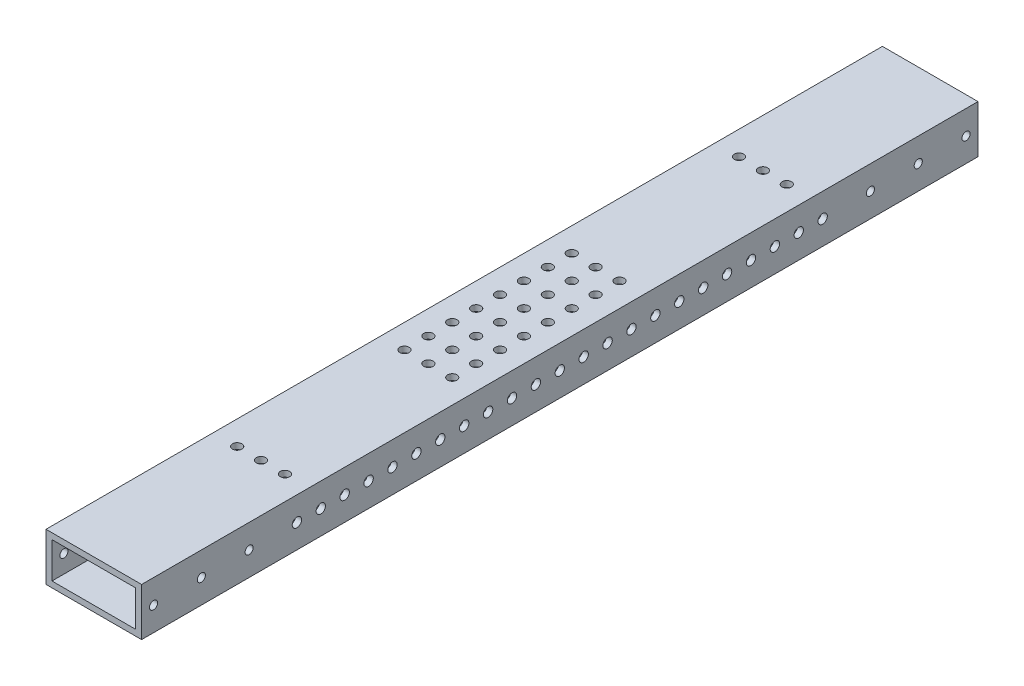
SolidWorks part; units mm, degrees
material "6061-T6 (SS)"
ref_plane "Front Plane" through (0, 0, 0) normal (0, 0, 1) x (1, 0, 0)
ref_plane "Top Plane" through (0, 0, 0) normal (0, 1, 0) x (1, 0, 0)
ref_plane "Right Plane" through (0, 0, 0) normal (1, 0, 0) x (0, 0, -1)
sketch "Sketch1" plane through (0, 0, 0) normal (0, 0, 1) x (1, 0, 0)
  line L0 (-22.225, 9.525) -> (22.225, 9.525)
  line L1 (-25.4, 12.7) -> (25.4, 12.7)
  line L2 (-25.4, 12.7) -> (-25.4, -12.7)
  line L3 (-25.4, -12.7) -> (25.4, -12.7)
  line L4 (25.4, 12.7) -> (25.4, -12.7)
  line L5 (22.225, 9.525) -> (22.225, -9.525)
  line L6 (-22.225, -9.525) -> (22.225, -9.525)
  line L7 (-22.225, 9.525) -> (-22.225, -9.525)
  line L8 (-25.4, 12.7) -> (25.4, -12.7) construction
  line L9 (25.4, 12.7) -> (-25.4, -12.7) construction
  point P5 (0, 0)
  dimension "D1" = 50.8
  dimension "D2" = 25.4
  dimension "D3" = 3.175
extrude "Boss-Extrude1" add sketch "Sketch1" along normal mid plane 444.5
sketch "Sketch3" plane through (25.4, 0, 0) normal (1, 0, 0) x (0, 0, -1)
  line L0 (-222.25, -12.7) -> (-222.25, 12.7) construction
  line L1 (-222.25, 12.7) -> (222.25, 12.7) construction
  line L2 (222.25, -12.7) -> (222.25, 12.7) construction
  circle A0 centre (-215.9, 0) radius 2.1527
  circle A1 centre (-190.5, 0) radius 2.1527
  circle A2 centre (-165.1, 0) radius 2.1527
  circle A3 centre (215.9, 0) radius 2.159
  circle A4 centre (190.5, 0) radius 2.159
  circle A5 centre (165.1, 0) radius 2.159
  dimension "D2" = 4.3053
  dimension "D9" = 4.318
  dimension "D1" = 6.35
  dimension "D3" = 12.7
  dimension "D4" = 31.75
  dimension "D5" = 12.7
  dimension "D6" = 57.15
  dimension "D7" = 12.7
  dimension "D8" = 6.35
  dimension "D10" = 12.7
  dimension "D11" = 31.75
  dimension "D12" = 57.15
  dimension "D13" = 12.7
  dimension "D14" = 12.7
extrude "Cut-Extrude2" cut sketch "Sketch3" against normal through all
sketch "Sketch4" plane through (25.4, 0, 0) normal (1, 0, 0) x (0, 0, -1)
  line L1 (-222.25, -12.7) -> (-222.25, 12.7) construction
  line L2 (-222.25, -12.7) -> (222.25, -12.7) construction
  circle A2 centre (-215.9, 0) radius 2.4892 construction
  circle A3 centre (-203.2, 0) radius 2.4892 construction
  circle A16 centre (-190.5, 0) radius 2.4892 construction
  circle A17 centre (-177.8, 0) radius 2.4892 construction
  circle A18 centre (-165.1, 0) radius 2.4892 construction
  circle A35 centre (-152.4, 0) radius 2.4892
  circle A36 centre (-139.7, 0) radius 2.4892
  circle A37 centre (-127, 0) radius 2.4892
  circle A38 centre (-114.3, 0) radius 2.4892
  circle A39 centre (-101.6, 0) radius 2.4892
  circle A40 centre (-88.9, 0) radius 2.4892
  circle A41 centre (-76.2, 0) radius 2.4892
  circle A42 centre (-63.5, 0) radius 2.4892
  circle A43 centre (-50.8, 0) radius 2.4892
  circle A44 centre (-38.1, 0) radius 2.4892
  circle A45 centre (-25.4, 0) radius 2.4892
  circle A46 centre (-12.7, 0) radius 2.4892
  circle A47 centre (0, 0) radius 2.4892
  circle A48 centre (12.7, 0) radius 2.4892
  circle A49 centre (25.4, 0) radius 2.4892
  circle A50 centre (38.1, 0) radius 2.4892
  circle A51 centre (50.8, 0) radius 2.4892
  circle A52 centre (63.5, 0) radius 2.4892
  circle A53 centre (76.2, 0) radius 2.4892
  circle A54 centre (88.9, 0) radius 2.4892
  circle A55 centre (101.6, 0) radius 2.4892
  circle A56 centre (114.3, 0) radius 2.4892
  circle A57 centre (127, 0) radius 2.4892
  circle A58 centre (139.7, 0) radius 2.4892
  circle A59 centre (152.4, 0) radius 2.4892
  circle A60 centre (165.1, 0) radius 2.4892 construction
  circle A61 centre (177.8, 0) radius 2.4892 construction
  circle A62 centre (190.5, 0) radius 2.4892 construction
  circle A63 centre (203.2, 0) radius 2.4892 construction
  dimension "D2" = 4.9784
  dimension "D1" = 6.35
  dimension "D3" = 12.7
  dimension "D4" = 12.7
  dimension "D5" = 34
extrude "Cut-Extrude3" cut sketch "Sketch4" against normal through all contours A36 | A37 | A38 | A39 | A40 | A41 | A42 | A43 | A44 | A45 | A46 | A47 | A48 | A49 | A50 | A51 | A52 | A53 | A54 | A55 | A56 | A57 | A58
sketch "Sketch5" plane through (0, -12.7, 0) normal (0, -1, 0) x (1, 0, 0)
  line L0 (-25.4, 0) -> (25.4, 0) construction
  line L4 (25.4, 222.25) -> (25.4, -222.25) construction
  line L5 (-25.4, 222.25) -> (-25.4, -222.25) construction
  line L6 (-25.4, 222.25) -> (25.4, 222.25) construction
  circle A0 centre (-12.7, 133.35) radius 2.4892
  circle A1 centre (0, 133.35) radius 2.4892
  circle A2 centre (12.7, 133.35) radius 2.4892
  circle A3 centre (12.7, -133.35) radius 2.4892
  circle A4 centre (0, -133.35) radius 2.4892
  circle A5 centre (-12.7, -133.35) radius 2.4892
  circle A6 centre (-12.7, 44.45) radius 2.4892
  circle A7 centre (0, 44.45) radius 2.4892
  circle A8 centre (12.7, 44.45) radius 2.4892
  circle A9 centre (12.7, 31.75) radius 2.4892
  circle A10 centre (0, 31.75) radius 2.4892
  circle A11 centre (-12.7, 31.75) radius 2.4892
  circle A12 centre (12.7, 19.05) radius 2.4892
  circle A13 centre (0, 19.05) radius 2.4892
  circle A14 centre (-12.7, 19.05) radius 2.4892
  circle A15 centre (12.7, 6.35) radius 2.4892
  circle A16 centre (0, 6.35) radius 2.4892
  circle A17 centre (-12.7, 6.35) radius 2.4892
  circle A18 centre (12.7, -6.35) radius 2.4892
  circle A19 centre (0, -6.35) radius 2.4892
  circle A20 centre (-12.7, -6.35) radius 2.4892
  circle A21 centre (12.7, -19.05) radius 2.4892
  circle A22 centre (0, -19.05) radius 2.4892
  circle A23 centre (-12.7, -19.05) radius 2.4892
  circle A24 centre (12.7, -31.75) radius 2.4892
  circle A25 centre (0, -31.75) radius 2.4892
  circle A26 centre (-12.7, -31.75) radius 2.4892
  circle A27 centre (12.7, -44.45) radius 2.4892
  circle A28 centre (0, -44.45) radius 2.4892
  circle A29 centre (-12.7, -44.45) radius 2.4892
  dimension "D1" = 4.9784
  dimension "D3" = 12.7
  dimension "D2" = 88.9
  dimension "D5" = 12.7
  dimension "D6" = 177.8
  dimension "D4" = 12.7
  dimension "D8" = 12.7
  dimension "D7" = 8
extrude "Cut-Extrude4" cut sketch "Sketch5" against normal through all
